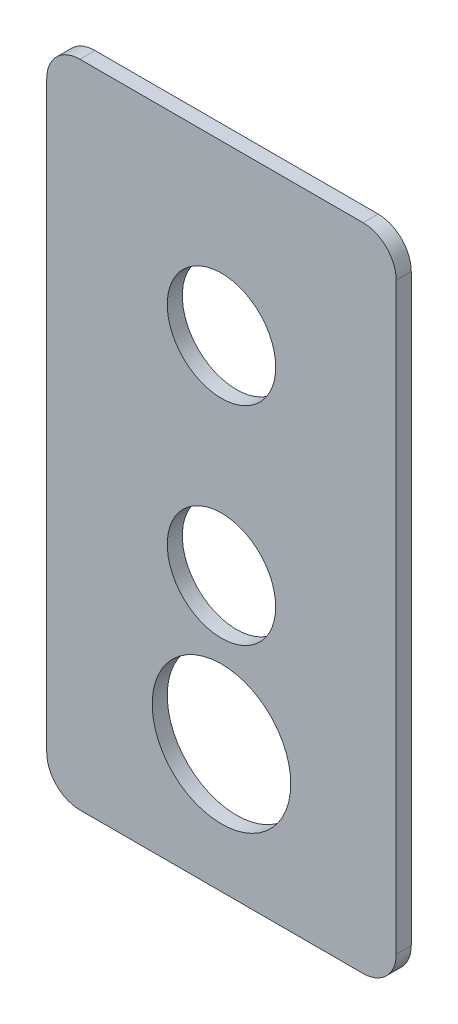
SolidWorks part; units mm, degrees
ref_plane "Front" through (0, 0, 0) normal (0, 0, 1) x (1, 0, 0)
ref_plane "Top" through (0, 0, 0) normal (0, 1, 0) x (1, 0, 0)
ref_plane "Right" through (0, 0, 0) normal (1, 0, 0) x (0, 0, -1)
sketch "Esboço1" plane through (0, 0, 0) normal (0, 1, 0) x (1, 0, 0)
  line L1 (-6.9603, -0.7727) -> (51.0397, -0.7727)
  line L2 (-6.9603, -0.7727) -> (-6.9603, -3.2727)
  line L3 (-6.9603, -3.2727) -> (51.0397, -3.2727)
  line L4 (51.0397, -0.7727) -> (51.0397, -3.2727)
  dimension "D1" = 2.5
  dimension "D2" = 58
extrude "Ressalto-extrusão1" add sketch "Esboço1" along normal blind 107.92
fillet "Filete1" radius 5.5 4 edges at (51.0397, 0, 2.0227) (-6.9603, 0, 2.0227) (-6.9603, 107.92, 2.0227) (51.0397, 107.92, 2.0227)
sketch "Esboço2" plane through (0, 0, 3.2727) normal (0, 0, 1) x (1, 0, 0)
  line L0 (-1.4603, 107.92) -> (45.5397, 107.92) construction
  circle A0 centre (22.0397, 79.92) radius 9
  circle A1 centre (22.0397, 45.4387) radius 9
  point P7 (22.0397, 107.92)
  dimension "D1" = 28
  dimension "D2" = 34.4813
  dimension "D3" = 18
  dimension "D4" = 18
extrude "Corte-extrusão1" cut sketch "Esboço2" against normal blind 111.42 contours A0 | A1
sketch "Esboço5" plane through (0, 0, 3.2727) normal (0, 0, 1) x (1, 0, 0)
  line L0 (-1.4603, 0) -> (45.5397, 0) construction
  circle A0 centre (22.0397, 21.2424) radius 11.5
  circle A1 centre (22.0397, 45.4387) radius 9 construction
  point P5 (22.0397, 0)
  dimension "D1" = 23
  dimension "D2" = 24.1963
extrude "Corte-extrusão2" cut sketch "Esboço5" against normal blind 111.42
sketch "Esboço6" plane through (0, 0, 0.7727) normal (0, 0, -1) x (-1, 0, 0)
  line L0 (-57.9332, 21.2424) -> (26.8819, 21.2424) construction
  line L1 (-57.9332, 5.7424) -> (26.8819, 5.7424) construction
  line L2 (-57.9332, 36.7424) -> (26.8819, 36.7424) construction
  line L3 (-22.0397, -6.7719) -> (-22.0397, 57.1759) construction
  line L4 (-6.5397, -6.7719) -> (-6.5397, 57.1759) construction
  line L5 (-37.5397, -6.7719) -> (-37.5397, 57.1759) construction
  dimension "D1" = 15.5
  dimension "D3" = 15.5
  dimension "D2" = 15.5
  dimension "D4" = 15.5
